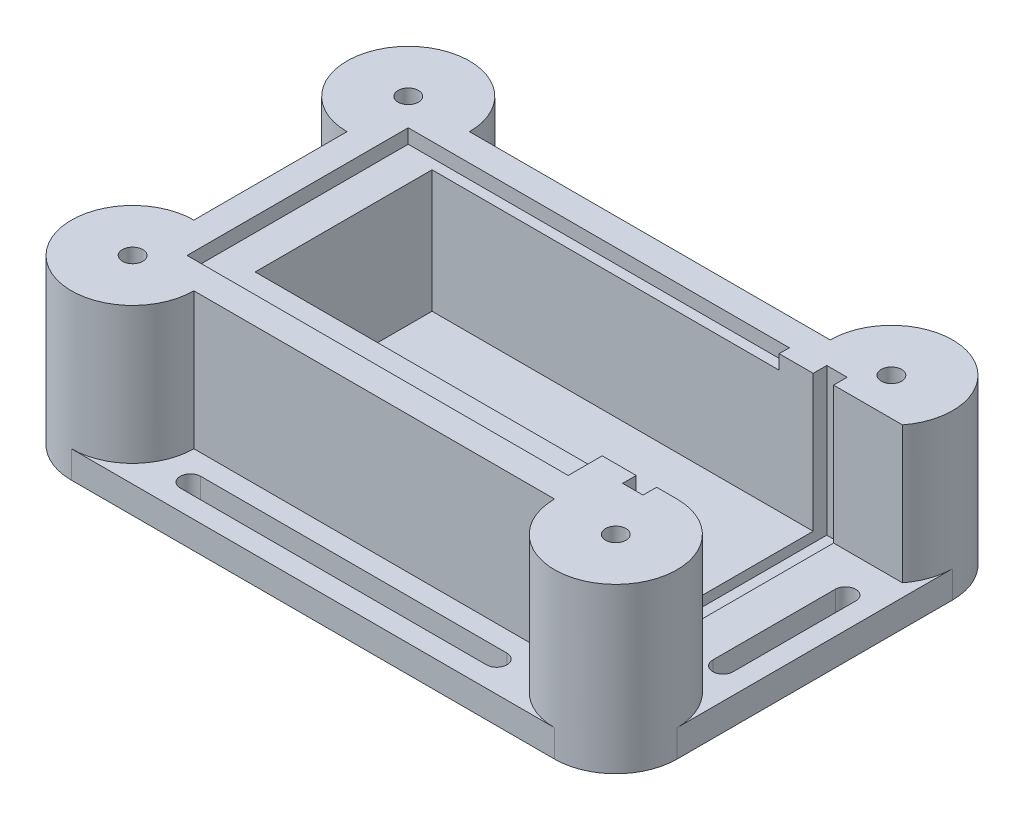
SolidWorks part; units mm, degrees
ref_plane "Front Plane" through (0, 0, 0) normal (0, 0, 1) x (1, 0, 0)
ref_plane "Top Plane" through (0, 0, 0) normal (0, 1, 0) x (1, 0, 0)
ref_plane "Right Plane" through (0, 0, 0) normal (1, 0, 0) x (0, 0, -1)
sketch "Sketch1" plane through (0, 0, 0) normal (1, 0, 0) x (0, 0, -1)
  line L0 (0, 0) -> (0, -18)
  line L1 (0, -18) -> (26, -18)
  line L2 (26, -18) -> (26, 0)
  line L3 (0, 0) -> (-5, 0)
  line L4 (-5, 0) -> (-5, 2.1)
  line L5 (-5, 2.1) -> (-9, 2.1)
  line L6 (26, 0) -> (27.5, 0)
  line L7 (27.5, 0) -> (27.5, 2.1)
  line L8 (27.5, 2.1) -> (31.5, 2.1)
  line L9 (-9, 2.1) -> (-9, -22)
  line L10 (-9, -22) -> (31.5, -22)
  line L11 (31.5, -22) -> (31.5, 2.1)
  dimension "D1" = 18
  dimension "D2" = 2.1
  dimension "D3" = 5
  dimension "D4" = 1.5
  dimension "D5" = 26
  dimension "D6" = 4
  dimension "D7" = 4
extrude "Boss-Extrude1" add sketch "Sketch1" against normal blind 56
sketch "Sketch2" plane through (-56, 0, 0) normal (-1, 0, 0) x (0, 0, 1)
  line L0 (9, 2.1) -> (9, -22) construction
  line L1 (9, -22) -> (-31.5, -22) construction
  line L2 (-31.5, -22) -> (-31.5, 2.1) construction
  line L3 (9, 2.1) -> (9, -22)
  line L4 (9, -22) -> (-31.5, -22)
  line L5 (-31.5, -22) -> (-31.5, 2.1)
  line L6 (-31.5, 2.1) -> (9, 2.1)
extrude "Boss-Extrude2" add sketch "Sketch2" along normal blind 4
sketch "Sketch3" plane through (-56, 0, 0) normal (1, 0, 0) x (0, 0, -1)
  line L0 (0, 0) -> (26, 0)
  line L8 (27.5, 0) -> (27.5, 2.1)
  line L9 (27.5, 2.1) -> (-5, 2.1)
  line L10 (-5, 2.1) -> (-5, 0)
  line L11 (-5, 0) -> (0, 0)
  line L12 (0, 0) -> (0, -18)
  line L13 (0, -18) -> (26, -18)
  line L14 (26, -18) -> (26, 0)
  line L15 (26, 0) -> (27.5, 0)
  line L20 (0, 0) -> (0, -18)
  line L21 (0, -18) -> (26, -18)
  line L22 (26, -18) -> (26, 0)
  dimension "D1" = 0
extrude "Boss-Extrude4" add sketch "Sketch3" along normal blind 5 contours L22 L21 L20 L0
sketch "Sketch5" plane through (0, 0, 0) normal (1, 0, 0) x (0, 0, -1)
  line L0 (0, 0) -> (0, 2.1)
  line L1 (-5, 2.1) -> (27.5, 2.1) construction
  line L2 (0, 2.1) -> (-5, 2.1)
  line L3 (26, 0) -> (26, 2.1)
  line L4 (26, 2.1) -> (27.5, 2.1)
  line L12 (0, 0) -> (-5, 0)
  line L13 (-5, 0) -> (-5, 2.1)
  line L14 (-5, 2.1) -> (-9, 2.1)
  line L15 (-9, 2.1) -> (-9, -22)
  line L16 (-9, -22) -> (31.5, -22)
  line L17 (31.5, -22) -> (31.5, 2.1)
  line L18 (31.5, 2.1) -> (27.5, 2.1)
  line L19 (27.5, 2.1) -> (27.5, 0)
  line L20 (27.5, 0) -> (26, 0)
  line L21 (26, 0) -> (26, -18)
  line L22 (26, -18) -> (0, -18)
  line L23 (0, -18) -> (0, 0)
  line L26 (-5, 2.1) -> (-9, 2.1)
  line L27 (-9, 2.1) -> (-9, -22)
  line L28 (-9, -22) -> (31.5, -22)
  line L29 (31.5, -22) -> (31.5, 2.1)
  line L30 (31.5, 2.1) -> (27.5, 2.1)
  line L33 (26, 0) -> (26, -18)
  line L34 (26, -18) -> (0, -18)
  line L35 (0, -18) -> (0, 0)
  dimension "D1" = 0
extrude "Boss-Extrude5" add sketch "Sketch5" along normal blind 11
sketch "Sketch6" plane through (0, 2.1, 0) normal (0, 1, 0) x (1, 0, 0)
  line L0 (11, 26) -> (0, 26) construction
  line L1 (5, -2) -> (8, -2)
  line L2 (5, -2) -> (5, 28)
  line L3 (5, 28) -> (8, 28)
  line L4 (8, -2) -> (8, 28)
  line L5 (-51, 0) -> (11, 0) construction
  line L6 (11, 31.5) -> (11, 26) construction
  dimension "D1" = 2
  dimension "D2" = 2
  dimension "D3" = 3
  dimension "D4" = 3
extrude "Cut-Extrude1" cut sketch "Sketch6" against normal offset from surface (21.6 mm away) 2.5 up to face at (-24.5, -22, -11.25)
sketch "Sketch4" plane through (0, -22, 0) normal (0, 1, 0) x (1, 0, 0)
  line L0 (-69, -9) -> (-69, 31.5)
  line L1 (-60, 11.25) -> (-60, -9)
  line L2 (-64.5, 20.25) -> (-64.5, 2.25) construction
  line L3 (-63, 20.25) -> (-63, 2.25)
  line L4 (-66, 20.25) -> (-66, 2.25)
  line L5 (-60, -9) -> (-60, 31.5) construction
  line L6 (-60, 31.5) -> (-60, 11.25)
  line L7 (-60, 31.5) -> (-51, 31.5)
  line L8 (-60, -9) -> (-51, -9)
  arc A0 (-51, 31.5) -> (-69, 31.5) centre (-60, 31.5) ccw
  arc A1 (-63, 20.25) -> (-66, 20.25) centre (-64.5, 20.25) ccw
  arc A2 (-66, 2.25) -> (-63, 2.25) centre (-64.5, 2.25) ccw
  arc A3 (-69, -9) -> (-51, -9) centre (-60, -9) ccw
  point P7 (-64.5, 11.25)
  point P12 (-69, 11.25)
  dimension "D1" = 3
  dimension "D3" = 1.5
  dimension "D4" = 18
  dimension "D2" = 3
sketch "Sketch7" plane through (0, -22, 0) normal (0, -1, 0) x (1, 0, 0)
  line L0 (-60, -22.5) -> (-60, -31.5)
  line L1 (-60, -31.5) -> (-51, -31.5)
  line L2 (2, -31.5) -> (11, -31.5)
  line L3 (11, -31.5) -> (11, -26)
  line L4 (11, -26) -> (18.1239, -26)
  line L5 (-60, 0) -> (-60, 9)
  line L6 (-60, 9) -> (-51, 9)
  line L7 (2, 9) -> (11, 9)
  line L8 (11, 9) -> (11, 0)
  arc A0 (-60, -22.5) -> (-51, -31.5) centre (-60, -31.5) ccw
  arc A1 (2, -31.5) -> (18.1239, -26) centre (11, -31.5) ccw
  arc A2 (-51, 9) -> (-60, 0) centre (-60, 9) ccw
  arc A3 (11, 0) -> (2, 9) centre (11, 9) ccw
extrude "Boss-Extrude6" add sketch "Sketch7" against normal up to surface (24.1 mm away) up to face at (-6.8, 2.1, -12.3)
sketch "Sketch8" plane through (0, -22, 0) normal (0, -1, 0) x (1, 0, 0)
  line L0 (-69, 9) -> (-69, -31.5)
  line L1 (-60, 0) -> (-60, -22.5)
  line L2 (-64.5, -20.25) -> (-64.5, -2.25) construction
  line L3 (-66, -20.25) -> (-66, -2.25)
  line L4 (-63, -20.25) -> (-63, -2.25)
  line L5 (-60, -40.5) -> (11, -40.5)
  line L6 (-47, -36) -> (-2, -36) construction
  line L7 (-47, -34.5) -> (-2, -34.5)
  line L8 (-47, -37.5) -> (-2, -37.5)
  line L9 (-51, -31.5) -> (2, -31.5) construction
  line L10 (20, -31.5) -> (20, 9)
  line L11 (15.5, -2.25) -> (15.5, -20.25) construction
  line L12 (17, -2.25) -> (17, -20.25)
  line L13 (14, -2.25) -> (14, -20.25)
  line L14 (11, -26) -> (11, 0) construction
  line L15 (-60, 18) -> (11, 18)
  line L16 (-47, 13.5) -> (-2, 13.5) construction
  line L17 (-47, 15) -> (-2, 15)
  line L18 (-47, 12) -> (-2, 12)
  line L19 (-51, 9) -> (2, 9) construction
  arc A0 (-66, -20.25) -> (-63, -20.25) centre (-64.5, -20.25) ccw
  arc A1 (-63, -2.25) -> (-66, -2.25) centre (-64.5, -2.25) ccw
  arc A2 (-69, -31.5) -> (-51, -31.5) centre (-60, -31.5) ccw construction
  arc A3 (2, -31.5) -> (18.1239, -26) centre (11, -31.5) ccw construction
  arc A4 (-47, -34.5) -> (-47, -37.5) centre (-47, -36) ccw
  arc A5 (-2, -37.5) -> (-2, -34.5) centre (-2, -36) ccw
  arc A6 (11, 0) -> (2, 9) centre (11, 9) ccw construction
  arc A7 (17, -2.25) -> (14, -2.25) centre (15.5, -2.25) ccw
  arc A8 (14, -20.25) -> (17, -20.25) centre (15.5, -20.25) ccw
  arc A9 (-51, 9) -> (-69, 9) centre (-60, 9) ccw construction
  arc A10 (-47, 15) -> (-47, 12) centre (-47, 13.5) ccw
  arc A11 (-2, 12) -> (-2, 15) centre (-2, 13.5) ccw
  arc A12 (-51, 9) -> (-60, 0) centre (-60, 9) ccw construction
  arc A13 (-60, -22.5) -> (-51, -31.5) centre (-60, -31.5) ccw construction
  arc A14 (20, 9) -> (11, 18) centre (11, 9) ccw
  arc A15 (11, -40.5) -> (20, -31.5) centre (11, -31.5) ccw
  arc A16 (-60, 18) -> (-69, 9) centre (-60, 9) ccw
  arc A17 (-69, -31.5) -> (-60, -40.5) centre (-60, -31.5) ccw
  point P12 (-64.5, -11.25)
  point P27 (-24.5, -36)
  point P35 (-24.5, -40.5)
  point P36 (-69, -11.25)
  point P43 (15.5, -11.25)
  point P52 (20, -11.25)
  point P53 (-24.5, 13.5)
  point P67 (-24.5, 18)
  line M27 (2, 9) -> (-51, 9)
  arc M28 (-51, 9) -> (-60, 0) centre (-60, 9) ccw
  line M29 (-60, 0) -> (-60, -22.5)
  arc M30 (-60, -22.5) -> (-51, -31.5) centre (-60, -31.5) ccw
  line M31 (-51, -31.5) -> (2, -31.5)
  arc M32 (2, -31.5) -> (18.1239, -26) centre (11, -31.5) ccw
  line M33 (18.1239, -26) -> (11, -26)
  line M34 (11, -26) -> (11, 0)
  arc M35 (11, 0) -> (2, 9) centre (11, 9) ccw
  dimension "D1" = 45
  dimension "D4" = 3
  dimension "D7" = 18
  dimension "D2" = 3
  dimension "D3" = 3
  dimension "D5" = 3
  dimension "D6" = 3
  dimension "D8" = 3
  dimension "D9" = 3
  dimension "D10" = 45
extrude "Boss-Extrude7" add sketch "Sketch8" against normal up to surface (4 mm away) contours L15 A11 L18 A10 L17 M28 M27 M35 | L10 A8 L13 A7 L12 M32 M35 M34 M33 | L5 A5 L8 A4 L7 M30 M32 M31 | L0 A1 L4 A0 L3 M28 M30 M29
sketch "Sketch9" plane through (0, 2.1, 0) normal (0, 1, 0) x (1, 0, 0)
  circle A0 centre (11, 31.5) radius 1.5
  circle A1 centre (-60, 31.5) radius 1.5
  circle A2 centre (-60, -9) radius 1.5
  circle A3 centre (11, -9) radius 1.5
  dimension "D1" = 3
extrude "Cut-Extrude2" cut sketch "Sketch9" against normal blind 20
